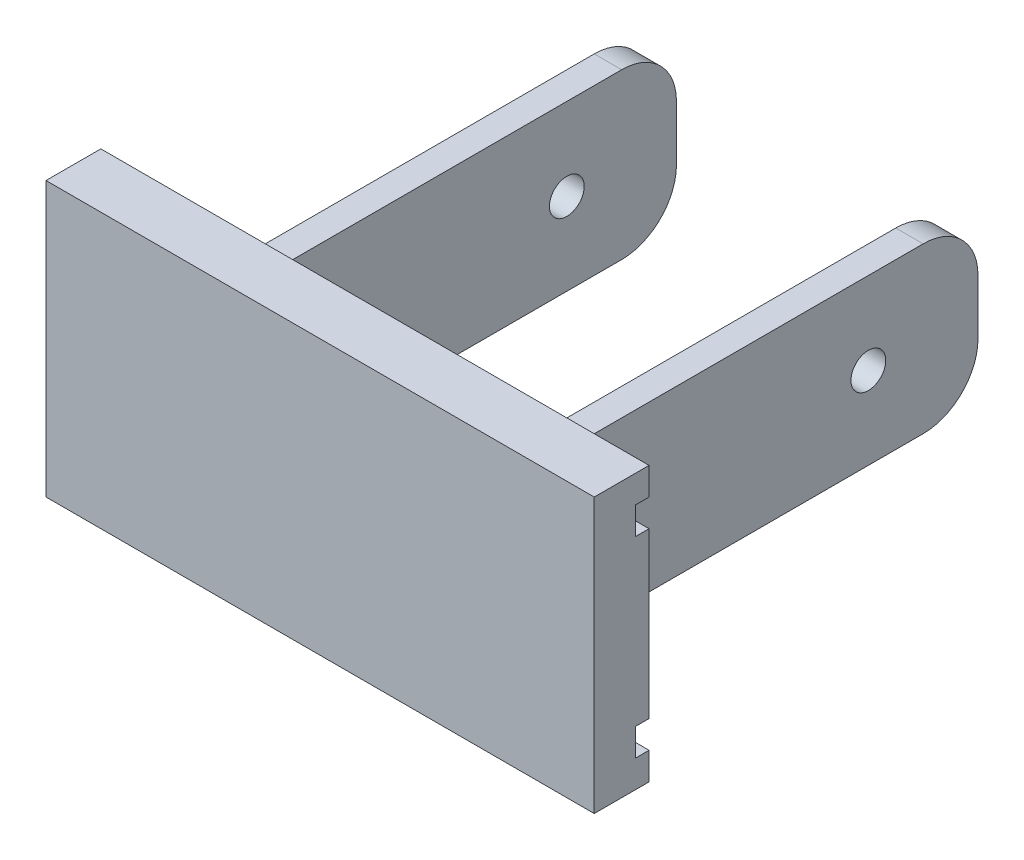
SolidWorks part; units mm, degrees
material "ABS"
ref_plane "Front Plane" through (0, 0, 0) normal (0, 0, 1) x (1, 0, 0)
ref_plane "Top Plane" through (0, 0, 0) normal (0, 1, 0) x (1, 0, 0)
ref_plane "Right Plane" through (0, 0, 0) normal (1, 0, 0) x (0, 0, -1)
sketch "Sketch1" plane through (0, 0, 0) normal (0, 0, 1) x (1, 0, 0)
  line L1 (0, 0) -> (100, 0)
  line L2 (0, 0) -> (0, 50)
  line L3 (0, 50) -> (100, 50)
  line L4 (100, 0) -> (100, 50)
  dimension "D1" = 100
  dimension "D2" = 50
extrude "Boss-Extrude1" add sketch "Sketch1" along normal blind 10
sketch "Sketch2" plane through (0, 0, 0) normal (-1, 0, 0) x (0, 0, 1)
  line L0 (0, 50) -> (0, 0) construction
  line L1 (0, 45) -> (2.5, 45)
  line L2 (0, 45) -> (0, 40)
  line L3 (0, 40) -> (2.5, 40)
  line L4 (2.5, 45) -> (2.5, 40)
  line L5 (10, 50) -> (0, 50) construction
  line L6 (0, 10) -> (2.5, 10)
  line L7 (0, 10) -> (0, 5)
  line L8 (0, 5) -> (2.5, 5)
  line L9 (2.5, 10) -> (2.5, 5)
  line L10 (10, 0) -> (0, 0) construction
  dimension "D1" = 5
  dimension "D2" = 10
  dimension "D3" = 5
  dimension "D4" = 10
  dimension "D5" = 2.5
  dimension "D6" = 2.5
extrude "Cut-Extrude1" cut sketch "Sketch2" against normal through all both and the other way through all
sketch "Sketch4" plane through (0, 0, 0) normal (0, 0, -1) x (-1, 0, 0)
  line L0 (-50, 50) -> (-50, 0) construction
  line L1 (-100, 50) -> (0, 50) construction
  line L2 (0, 0) -> (-100, 0) construction
  line L3 (-80, 40) -> (-80, 10)
  line L4 (-100, 40) -> (0, 40) construction
  line L5 (-100, 10) -> (0, 10) construction
  line L6 (-80, 10) -> (-75, 10)
  line L7 (-75, 10) -> (-75, 40)
  line L8 (-100, 40) -> (0, 40) construction
  line L9 (-75, 40) -> (-80, 40)
  line L10 (-25, 10) -> (-25, 40)
  line L11 (-20, 10) -> (-25, 10)
  line L12 (-20, 40) -> (-20, 10)
  line L13 (-25, 40) -> (-20, 40)
  dimension "D1" = 5
  dimension "D2" = 25
extrude "Boss-Extrude2" add sketch "Sketch4" along normal blind 80
sketch "Sketch5" plane through (80, 0, 0) normal (1, 0, 0) x (0, 0, -1)
  line L0 (0, 25) -> (80.3437, 25) construction
  line L1 (0, 10) -> (0, 40) construction
  circle A1 centre (60, 25) radius 3.1732
  dimension "D1" = 60
extrude "Cut-Extrude3" cut sketch "Sketch5" against normal through all both and the other way through all
fillet "Fillet1" radius 10 4 edges at (22.5, 10, -80) (77.5, 10, -80) (77.5, 40, -80) (22.5, 40, -80)
fillet "Fillet2" radius 10 2 edges at (80, 25, 0) (20, 25, 0)
